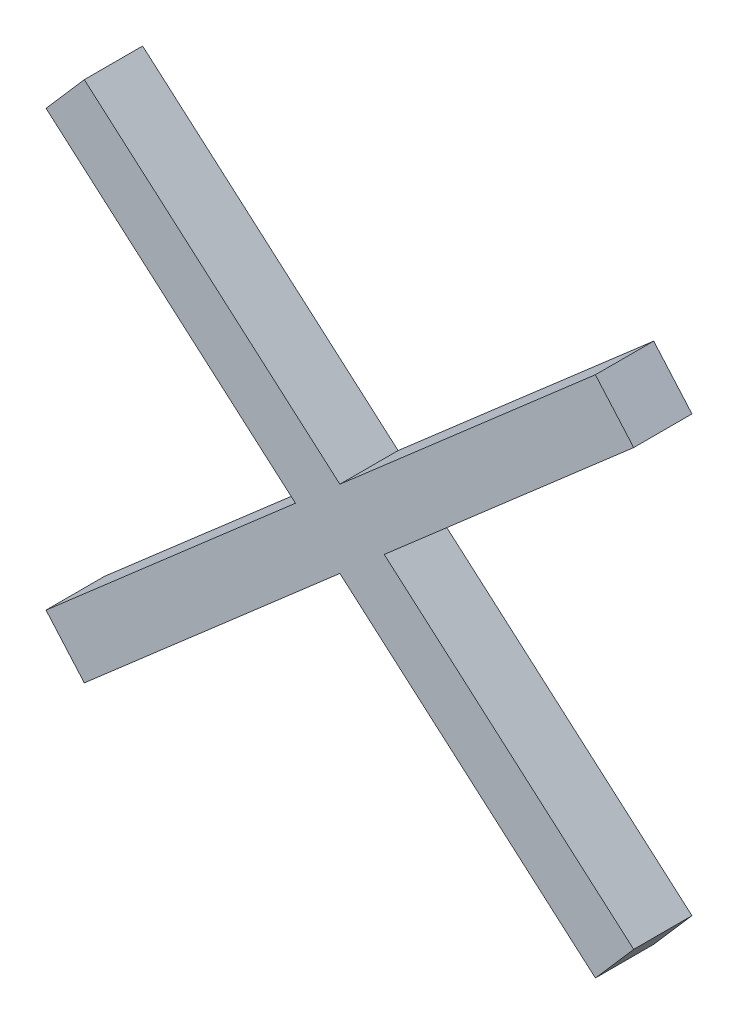
SolidWorks part; units mm, degrees
ref_plane "Front Plane" through (0, 0, 0) normal (0, 0, 1) x (1, 0, 0)
ref_plane "Top Plane" through (0, 0, 0) normal (0, 1, 0) x (1, 0, 0)
ref_plane "Right Plane" through (0, 0, 0) normal (1, 0, 0) x (0, 0, -1)
sketch "Sketch1" plane through (0, 0, 0) normal (0, 0, 1) x (1, 0, 0)
  line L0 (-10.4352, 0.0942) -> (1.5258, -10.3235) construction
  line L1 (-15.5, -13.5) -> (15.5, -13.5) construction
  line L2 (-15.5, -13.5) -> (-15.5, 13.5) construction
  line L3 (-15.5, 13.5) -> (15.5, 13.5) construction
  line L4 (15.5, -13.5) -> (15.5, 13.5) construction
  line L5 (-15.5, -13.5) -> (15.5, 13.5) construction
  line L6 (-15.5, 13.5) -> (15.5, -13.5) construction
  line L7 (-10.4352, 0.0942) -> (-1.5258, 10.3235) construction
  line L8 (1.5258, -10.3235) -> (10.4352, -0.0942) construction
  line L9 (-1.5258, 10.3235) -> (10.4352, -0.0942) construction
  line L10 (-10.4352, 0.0942) -> (10.4352, -0.0942) construction
  line L11 (1.5258, -10.3235) -> (-1.5258, 10.3235) construction
  line L12 (-20.1656, 14.9114) -> (-17.5385, 17.9277)
  line L13 (-20.1656, 14.9114) -> (17.5385, -17.9277)
  line L14 (-17.5385, 17.9277) -> (20.1656, -14.9114)
  line L15 (17.5385, -17.9277) -> (20.1656, -14.9114)
  line L16 (-20.1656, 14.9114) -> (20.1656, -14.9114) construction
  line L17 (-17.5385, 17.9277) -> (17.5385, -17.9277) construction
  line L18 (-3.0745, -9.9092) -> (10.2374, 1.6851) construction
  line L19 (-3.0745, -9.9092) -> (-10.2374, -1.6851) construction
  line L20 (10.2374, 1.6851) -> (3.0745, 9.9092) construction
  line L21 (-10.2374, -1.6851) -> (3.0745, 9.9092) construction
  line L22 (-3.0745, -9.9092) -> (3.0745, 9.9092) construction
  line L23 (10.2374, 1.6851) -> (-10.2374, -1.6851) construction
  line L24 (-17.5385, -17.9277) -> (-20.1656, -14.9114)
  line L25 (-17.5385, -17.9277) -> (20.1656, 14.9114)
  line L26 (-20.1656, -14.9114) -> (17.5385, 17.9277)
  line L27 (20.1656, 14.9114) -> (17.5385, 17.9277)
  line L28 (-17.5385, -17.9277) -> (17.5385, 17.9277) construction
  line L29 (-20.1656, -14.9114) -> (20.1656, 14.9114) construction
  point P0 (0, 0)
  point P6 (0, 0)
  point P7 (0, 0)
  point P8 (0, 0)
  point P13 (0, 0)
  dimension "D1" = 27
  dimension "D2" = 31
  dimension "D3" = 50
  dimension "D4" = 50
  dimension "D5" = 4
  dimension "D6" = 4
extrude "Boss-Extrude1" add sketch "Sketch1" along normal blind 4 contours L25 L27 L26 L24 | L13 L15 L14 L12
equation "\"D1@Boss-Extrude1\"=\"mat@V1.assembly\""
